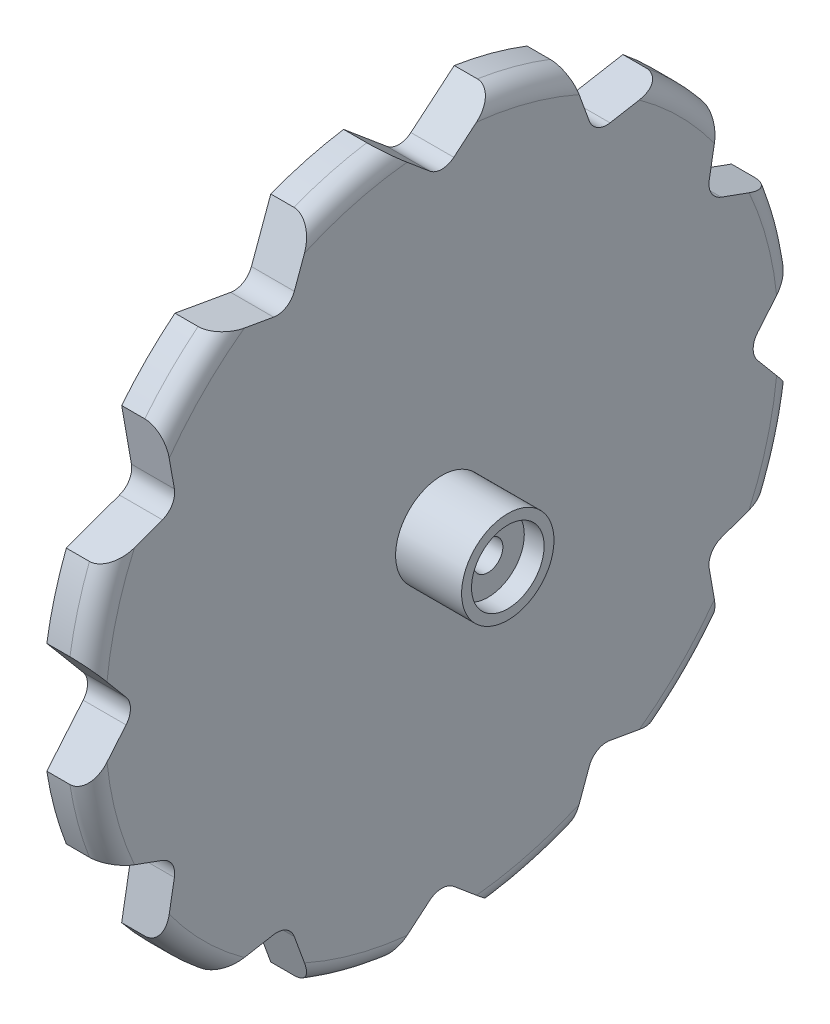
SolidWorks part; units mm, degrees
ref_plane "Спереди" through (0, 0, 0) normal (0, 0, 1) x (1, 0, 0)
ref_plane "Сверху" through (0, 0, 0) normal (0, 1, 0) x (1, 0, 0)
ref_plane "Справа" through (0, 0, 0) normal (1, 0, 0) x (0, 0, -1)
sketch "Sketch1" plane through (0, 0, 0) normal (1, 0, 0) x (0, 0, -1)
  line L0 (1.8159, 47.8359) -> (8.3819, 53.3455)
  line L25 (19.4138, 50.3895) -> (22.3454, 42.3351)
  line L26 (25.4906, 40.5192) -> (33.9317, 42.0076)
  line L27 (42.0076, 33.9317) -> (40.5192, 25.4906)
  line L28 (42.3351, 22.3454) -> (50.3895, 19.4138)
  line L29 (53.3455, 8.3819) -> (47.8359, 1.8159)
  line L30 (47.8359, -1.8159) -> (53.3455, -8.3819)
  line L31 (50.3895, -19.4138) -> (42.3351, -22.3454)
  line L32 (40.5192, -25.4906) -> (42.0076, -33.9317)
  line L33 (33.9317, -42.0076) -> (25.4906, -40.5192)
  line L34 (22.3454, -42.3351) -> (19.4138, -50.3895)
  line L35 (8.3819, -53.3455) -> (1.8159, -47.8359)
  line L36 (-1.8159, -47.8359) -> (-8.3819, -53.3455)
  line L37 (-19.4138, -50.3895) -> (-22.3454, -42.3351)
  line L38 (-25.4906, -40.5192) -> (-33.9317, -42.0076)
  line L39 (-42.0076, -33.9317) -> (-40.5192, -25.4906)
  line L40 (-42.3351, -22.3454) -> (-50.3895, -19.4138)
  line L41 (-53.3455, -8.3819) -> (-47.8359, -1.8159)
  line L42 (-47.8359, 1.8159) -> (-53.3455, 8.3819)
  line L43 (-50.3895, 19.4138) -> (-42.3351, 22.3454)
  line L44 (-40.5192, 25.4906) -> (-42.0076, 33.9317)
  line L45 (-33.9317, 42.0076) -> (-25.4906, 40.5192)
  line L46 (-22.3454, 42.3351) -> (-19.4138, 50.3895)
  line L47 (-8.3819, 53.3455) -> (-1.8159, 47.8359)
  line L48 (0, 0) -> (0, 50) construction
  circle A25 centre (0, 0) radius 50 construction
  arc A26 (-1.8159, 47.8359) -> (1.8159, 47.8359) centre (0, 50) ccw
  arc A27 (22.3454, 42.3351) -> (25.4906, 40.5192) centre (25, 43.3013) ccw
  arc A28 (40.5192, 25.4906) -> (42.3351, 22.3454) centre (43.3013, 25) ccw
  arc A29 (47.8359, 1.8159) -> (47.8359, -1.8159) centre (50, 0) ccw
  arc A30 (42.3351, -22.3454) -> (40.5192, -25.4906) centre (43.3013, -25) ccw
  arc A31 (25.4906, -40.5192) -> (22.3454, -42.3351) centre (25, -43.3013) ccw
  arc A32 (1.8159, -47.8359) -> (-1.8159, -47.8359) centre (0, -50) ccw
  arc A33 (-22.3454, -42.3351) -> (-25.4906, -40.5192) centre (-25, -43.3013) ccw
  arc A34 (-40.5192, -25.4906) -> (-42.3351, -22.3454) centre (-43.3013, -25) ccw
  arc A35 (-47.8359, -1.8159) -> (-47.8359, 1.8159) centre (-50, 0) ccw
  arc A36 (-42.3351, 22.3454) -> (-40.5192, 25.4906) centre (-43.3013, 25) ccw
  arc A37 (-25.4906, 40.5192) -> (-22.3454, 42.3351) centre (-25, 43.3013) ccw
  arc A38 (-50.3895, 19.4138) -> (-53.3455, 8.3819) centre (0, 0) ccw
  arc A39 (-53.3455, -8.3819) -> (-50.3895, -19.4138) centre (0, 0) ccw
  arc A40 (-42.0076, -33.9317) -> (-33.9317, -42.0076) centre (0, 0) ccw
  arc A41 (-19.4138, -50.3895) -> (-8.3819, -53.3455) centre (0, 0) ccw
  arc A42 (8.3819, -53.3455) -> (19.4138, -50.3895) centre (0, 0) ccw
  arc A43 (33.9317, -42.0076) -> (42.0076, -33.9317) centre (0, 0) ccw
  arc A44 (50.3895, -19.4138) -> (53.3455, -8.3819) centre (0, 0) ccw
  arc A45 (53.3455, 8.3819) -> (50.3895, 19.4138) centre (0, 0) ccw
  arc A46 (42.0076, 33.9317) -> (33.9317, 42.0076) centre (0, 0) ccw
  arc A47 (19.4138, 50.3895) -> (8.3819, 53.3455) centre (0, 0) ccw
  arc A48 (-8.3819, 53.3455) -> (-19.4138, 50.3895) centre (0, 0) ccw
  arc A49 (-33.9317, 42.0076) -> (-42.0076, 33.9317) centre (0, 0) ccw
  dimension "D1" = 2.825
  dimension "D2" = 100
  dimension "D5" = 108
  dimension "D4" = 12
  dimension "D3" = 50
extrude "Boss-Extrude1" add sketch "Sketch1" along normal blind 6.5
sketch "Sketch2" plane through (6.5, 0, 0) normal (1, 0, 0) x (0, 0, -1)
  circle A0 centre (0, 0) radius 7
  point P3 (0, 0)
  dimension "D1" = 14
extrude "Boss-Extrude2" add sketch "Sketch2" along normal blind 10
sketch "Sketch3" plane through (16.5, 0, 0) normal (1, 0, 0) x (0, 0, -1)
  circle A0 centre (0, 0) radius 5.5
  dimension "D1" = 11
extrude "Cut-Extrude1" cut sketch "Sketch3" against normal blind 3
sketch "Sketch4" plane through (0, 0, 0) normal (-1, 0, 0) x (0, 0, 1)
  circle A0 centre (0, 0) radius 2.25
  dimension "D1" = 4.5
extrude "Cut-Extrude2" cut sketch "Sketch4" against normal through all both and the other way through all
fillet "Fillet1" radius 3 12 edges at (6.5, -13.9762, -52.16) (6.5, -38.1838, -38.1838) (6.5, -52.16, -13.9762) (6.5, -52.16, 13.9762) (6.5, -38.1838, 38.1838) (6.5, -13.9762, 52.16) (6.5, 13.9762, 52.16) (6.5, 38.1838, 38.1838) (6.5, 52.16, 13.9762) (6.5, 52.16, -13.9762) (6.5, 13.9762, -52.16) (6.5, 38.1838, -38.1838)
sketch "Sketch5" plane through (0, 0, 0) normal (-1, 0, 0) x (0, 0, 1)
  line L0 (0, 50) -> (-25, 43.3013) construction
